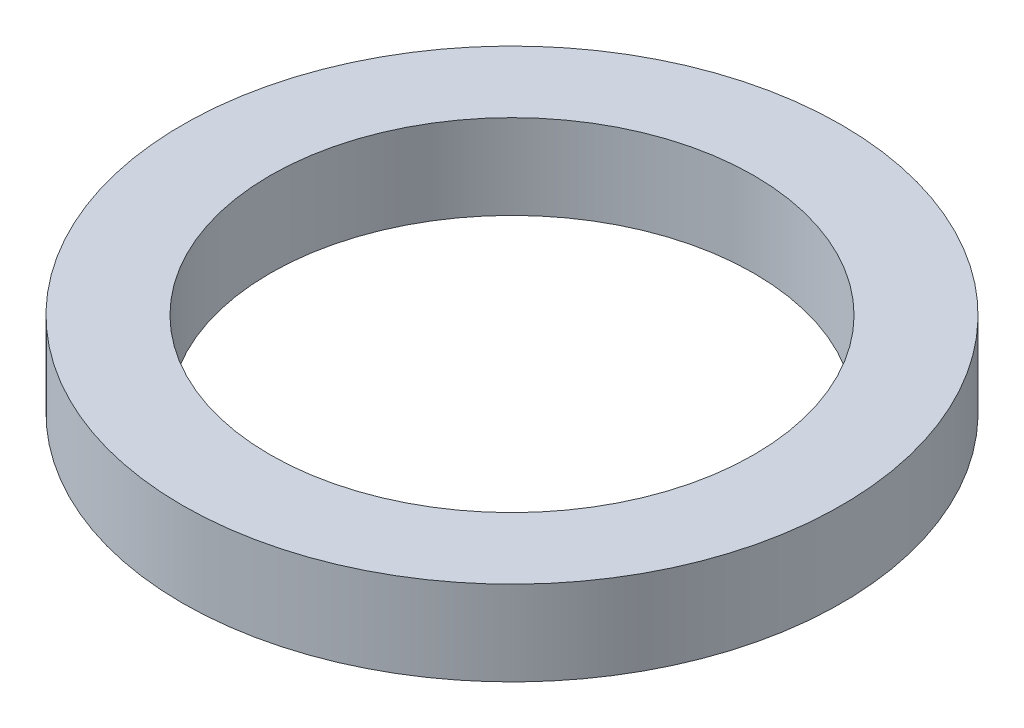
SolidWorks part; units mm, degrees
ref_plane "Front Plane" through (0, 0, 0) normal (0, 0, 1) x (1, 0, 0)
ref_plane "Top Plane" through (0, 0, 0) normal (0, 1, 0) x (1, 0, 0)
ref_plane "Right Plane" through (0, 0, 0) normal (1, 0, 0) x (0, 0, -1)
sketch "Sketch1" plane through (0, 0, 0) normal (0, 1, 0) x (1, 0, 0)
  circle A0 centre (0, 0) radius 8
  circle A1 centre (0, 0) radius 10.9
  dimension "D1" = 16
  dimension "D2" = 2.9
extrude "Boss-Extrude1" add sketch "Sketch1" along normal blind 2.8
